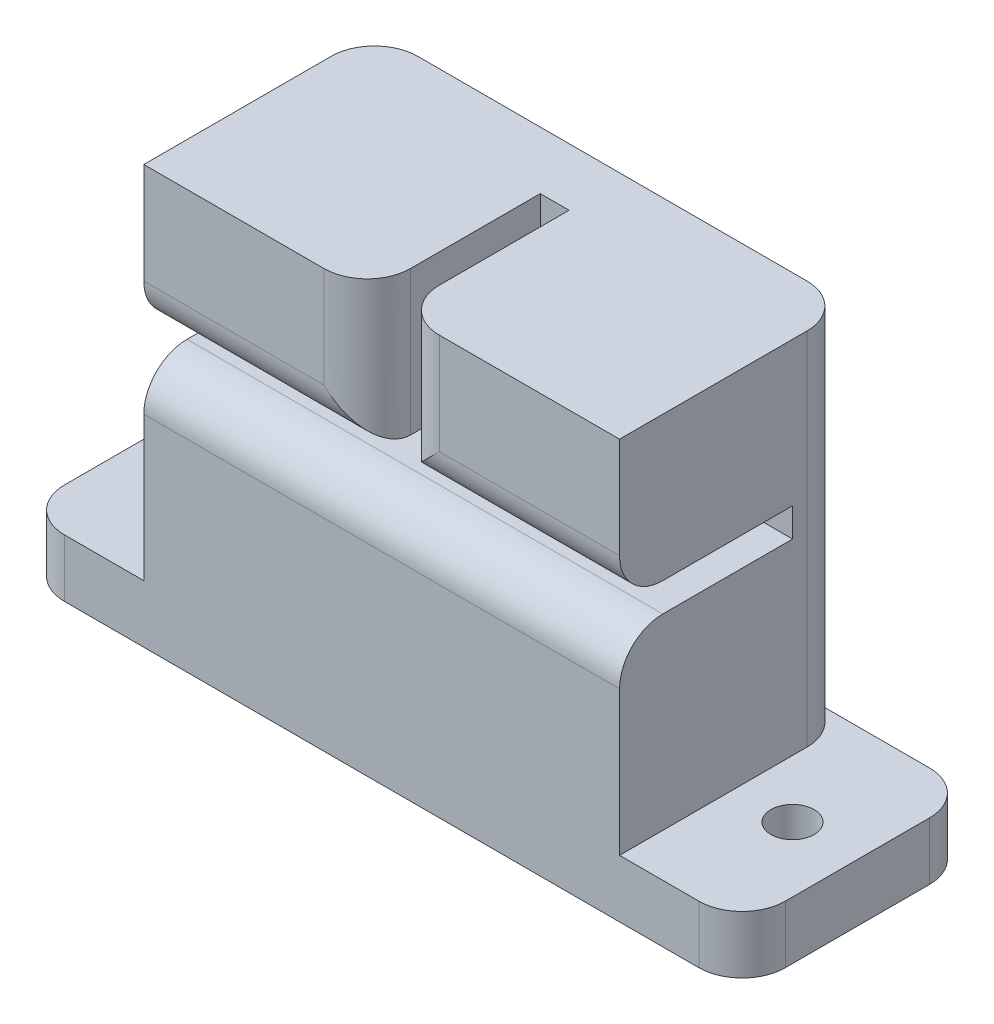
SolidWorks part; units mm, degrees
material "ABS generico"
ref_plane "Front Plane" through (0, 0, 0) normal (0, 0, 1) x (1, 0, 0)
ref_plane "Top Plane" through (0, 0, 0) normal (0, 1, 0) x (1, 0, 0)
ref_plane "Right Plane" through (0, 0, 0) normal (1, 0, 0) x (0, 0, -1)
sketch "Sketch1" plane through (0, 0, 0) normal (0, 0, 1) x (1, 0, 0)
  line L0 (-25, -14.5) -> (25, -14.5)
  line L1 (-16.5, 14.5) -> (16.5, 14.5)
  line L2 (-16.5, 14.5) -> (-16.5, -10.5)
  line L3 (-16.5, -14.5) -> (16.5, -14.5)
  line L4 (16.5, 14.5) -> (16.5, -10.5)
  line L5 (-16.5, 14.5) -> (16.5, -14.5) construction
  line L6 (-16.5, -14.5) -> (16.5, 14.5) construction
  line L7 (-25, -10.5) -> (-16.5, -10.5)
  line L8 (0, -22.0017) -> (0, 34.5889) construction
  line L9 (25, -14.5) -> (25, -10.5)
  line L10 (-25, -14.5) -> (-25, -10.5)
  line L11 (16.5, -10.5) -> (25, -10.5)
  line L12 (-25, -22.0017) -> (-25, 34.5889) construction
  line L13 (-48.5805, -10.5) -> (62.5201, -10.5) construction
  line L14 (-48.5805, -14.5) -> (62.5201, -14.5) construction
  line L16 (25, -22.0017) -> (25, 34.5889) construction
  point P0 (0, 0)
  dimension "D1" = 33
  dimension "D2" = 29
  dimension "D3" = 4
  dimension "D4" = 25
  dimension "D5" = 25
extrude "Extrude1" add sketch "Sketch1" against normal blind 16 contours L11 L4 L1 L2 L7 L10 L0 L9
sketch "Sketch2" plane through (0, 0, 0) normal (0, 0, 1) x (1, 0, 0)
  line L0 (-1, 14.5) -> (1, 14.5)
  line L1 (-16.5, 2.5) -> (16.5, 2.5)
  line L2 (-16.5, 26.5) -> (29.5295, 26.5)
  line L3 (-16.5, 4.5) -> (-1, 4.5)
  line L4 (0, 1.9361) -> (0, 14.5) construction
  line L6 (-16.5, 2.5) -> (29.5295, 2.5) construction
  line L7 (-16.5, 4.5) -> (-16.5, 2.5)
  line L8 (16.5, 4.5) -> (16.5, 2.5)
  line L10 (1, 4.5) -> (1, 14.5)
  line L11 (-16.5, 14.5) -> (29.5295, 14.5) construction
  line L15 (1, 4.5) -> (16.5, 4.5)
  line L16 (-1, 4.5) -> (-1, 14.5)
  line L17 (-16.5, 4.5) -> (29.5295, 4.5) construction
  point P10 (0, 16.737)
  point P12 (1, 1.9361)
  point P13 (1, 16.737)
  point P14 (-1, 1.9361)
  point P15 (-1, 16.737)
  line M5 (16.5, -10.5) -> (16.5, 14.5)
  line M6 (16.5, 14.5) -> (-16.5, 14.5)
  line M7 (-16.5, 14.5) -> (-16.5, -10.5)
  dimension "D1" = 12
  dimension "D2" = 2
extrude "Extrude6" cut sketch "Sketch2" against normal blind 12 contours L16 L3 L1 L15 L10 M7 M5 M6
sketch "Sketch3" plane through (0, -14.5, 0) normal (0, -1, 0) x (1, 0, 0)
  line L0 (-25, -8) -> (25, -8) construction
  line L1 (-25, -16) -> (-25, 0) construction
  line L2 (25, -16) -> (25, 0) construction
  line L3 (0, 6.24) -> (0, -19.7792) construction
  circle A0 centre (-20.5, -8) radius 1.5
  circle A1 centre (20.5, -8) radius 1.5
  dimension "D2" = 3
  dimension "D1" = 20.5
extrude "Extrude7" cut sketch "Sketch3" against normal up to surface (4 mm away) up to face at (20.75, -10.5, -8)
fillet "Fillet1" radius 3 5 edges at (-1, 9.5, 0) (-8.75, 4.5, 0) (0, 2.5, 0) (8.75, 4.5, 0) (1, 9.5, 0)
fillet "Fillet2" radius 3 6 edges at (16.5, 2, -16) (-16.5, 2, -16) (-25, -12.5, -16) (-25, -12.5, 0) (25, -12.5, -16) (25, -12.5, 0)
